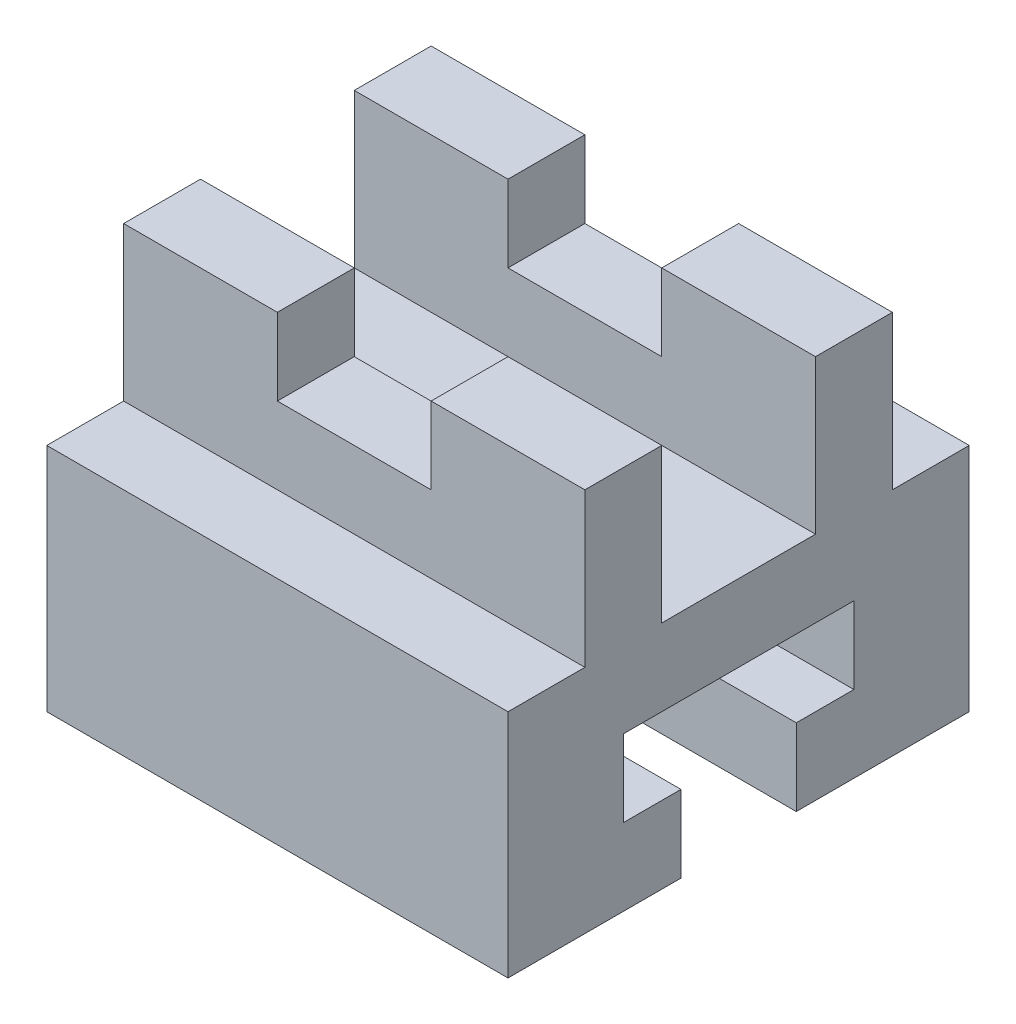
SolidWorks part; units mm, degrees
ref_plane "Front Plane" through (0, 0, 0) normal (0, 0, 1) x (1, 0, 0)
ref_plane "Top Plane" through (0, 0, 0) normal (0, 1, 0) x (1, 0, 0)
ref_plane "Right Plane" through (0, 0, 0) normal (1, 0, 0) x (0, 0, -1)
sketch "Sketch2" plane through (0, 0, 0) normal (0, 0, 1) x (1, 0, 0)
  line L0 (-27.2973, -10.2027) -> (32.7027, -10.2027)
  line L1 (32.7027, -10.2027) -> (32.7027, 39.7973)
  line L2 (32.7027, 39.7973) -> (-27.2973, 39.7973)
  line L3 (-27.2973, 39.7973) -> (-27.2973, -10.2027)
  dimension "D1" = 60
  dimension "D2" = 50
extrude "Boss-Extrude2" add sketch "Sketch2" along normal blind 60
sketch "Sketch4" plane through (-27.2973, 0, 0) normal (-1, 0, 0) x (0, 0, 1)
  line L0 (10, 39.7973) -> (10, 19.7973)
  line L1 (60, 39.7973) -> (0, 39.7973) construction
  line L2 (10, 19.7973) -> (0, 19.7973)
  line L3 (0, 39.7973) -> (0, -10.2027) construction
  line L4 (0, 19.7973) -> (0, 39.7973)
  line L5 (0, 39.7973) -> (10, 39.7973)
  line L6 (50, 39.7973) -> (50, 19.7973)
  line L7 (50, 19.7973) -> (60, 19.7973)
  line L8 (60, 39.7973) -> (60, -10.2027) construction
  line L9 (60, 19.7973) -> (60, 39.7973)
  line L10 (60, 39.7973) -> (50, 39.7973)
  dimension "D1" = 10
  dimension "D2" = 20
  dimension "D3" = 10
  dimension "D4" = 20
extrude "Cut-Extrude2" cut sketch "Sketch4" against normal blind 60
sketch "Sketch7" plane through (32.7027, 0, 0) normal (1, 0, 0) x (0, 0, -1)
  line L0 (-37.5, -10.2027) -> (-37.5, -0.2027)
  line L1 (-60, -10.2027) -> (0, -10.2027) construction
  line L2 (-37.5, -0.2027) -> (-45, -0.2027)
  line L3 (-45, -0.2027) -> (-45, 9.7973)
  line L4 (-45, 9.7973) -> (-15, 9.7973)
  line L5 (-15, 9.7973) -> (-15, -0.2027)
  line L6 (-15, -0.2027) -> (-22.5, -0.2027)
  line L7 (-22.5, -0.2027) -> (-22.5, -10.2027)
  line L8 (-22.5, -10.2027) -> (-37.5, -10.2027)
  line L9 (-60, -10.2027) -> (-60, 19.7973) construction
  dimension "D1" = 15
  dimension "D2" = 30
  dimension "D3" = 10
  dimension "D4" = 7.5
  dimension "D5" = 22.5
  dimension "D6" = 20
extrude "Cut-Extrude4" cut sketch "Sketch7" against normal blind 60
sketch "Sketch8" plane through (-27.2973, 0, 0) normal (-1, 0, 0) x (0, 0, 1)
  line L0 (20, 39.7973) -> (20, 19.7973)
  line L1 (50, 39.7973) -> (10, 39.7973) construction
  line L2 (20, 19.7973) -> (40, 19.7973)
  line L3 (40, 19.7973) -> (40, 39.7973)
  line L4 (40, 39.7973) -> (20, 39.7973)
  dimension "D1" = 20
  dimension "D2" = 20
  dimension "D3" = 20
extrude "Cut-Extrude5" cut sketch "Sketch8" against normal blind 60
sketch "Sketch9" plane through (0, 0, 50) normal (0, 0, 1) x (1, 0, 0)
  line L0 (-7.2973, 39.7973) -> (12.7027, 39.7973)
  line L1 (32.7027, 39.7973) -> (-27.2973, 39.7973) construction
  line L2 (12.7027, 39.7973) -> (12.7027, 29.7973)
  line L3 (12.7027, 29.7973) -> (-7.2973, 29.7973)
  line L4 (-7.2973, 29.7973) -> (-7.2973, 39.7973)
  dimension "D1" = 20
  dimension "D2" = 10
  dimension "D3" = 20
extrude "Cut-Extrude6" cut sketch "Sketch9" against normal blind 40
sketch "Sketch10" plane through (32.7027, 0, 0) normal (1, 0, 0) x (0, 0, -1)
